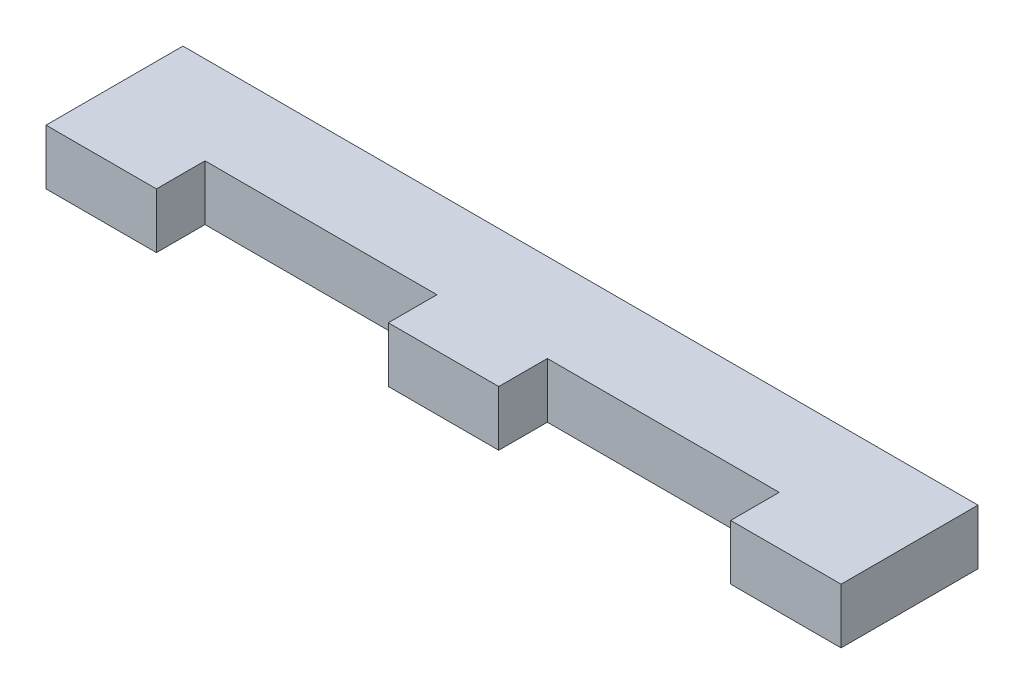
SolidWorks part; units mm, degrees
ref_plane "Front Plane" through (0, 0, 0) normal (0, 0, 1) x (1, 0, 0)
ref_plane "Top Plane" through (0, 0, 0) normal (0, 1, 0) x (1, 0, 0)
ref_plane "Right Plane" through (0, 0, 0) normal (1, 0, 0) x (0, 0, -1)
sketch "Sketch1" plane through (0, 0, 0) normal (0, 1, 0) x (1, 0, 0)
  line L0 (-6.35, -5.08) -> (-6.35, -10.668)
  line L1 (-33.02, -5.08) -> (-6.35, -5.08)
  line L2 (-45.72, -5.08) -> (-45.72, 5.08)
  line L3 (-45.72, 5.08) -> (45.72, 5.08)
  line L4 (45.72, -5.08) -> (45.72, 5.08)
  line L5 (-45.72, -5.08) -> (45.72, 5.08) construction
  line L6 (-45.72, 5.08) -> (45.72, -5.08) construction
  line L7 (6.35, -5.08) -> (33.02, -5.08)
  line L8 (-45.72, -5.08) -> (-45.72, -10.668)
  line L9 (-45.72, -10.668) -> (-33.02, -10.668)
  line L10 (-33.02, -5.08) -> (-33.02, -10.668)
  line L11 (-6.35, -10.668) -> (6.35, -10.668)
  line L12 (6.35, -5.08) -> (6.35, -10.668)
  line L13 (33.02, -5.08) -> (33.02, -10.668)
  line L14 (33.02, -10.668) -> (45.72, -10.668)
  line L15 (45.72, -5.08) -> (45.72, -10.668)
  point P0 (0, 0)
  dimension "D1" = 91.44
  dimension "D2" = 10.16
  dimension "D3" = 5.588
  dimension "D4" = 12.7
  dimension "D5" = 3
extrude "Boss-Extrude1" add sketch "Sketch1" along normal blind 6.35
